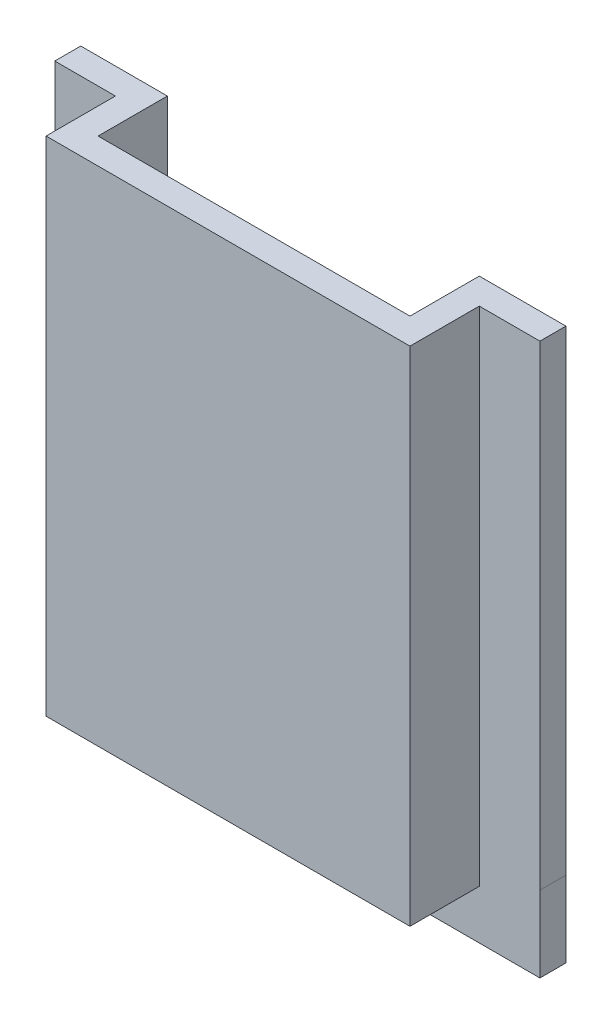
SolidWorks part; units mm, degrees
ref_plane "Front Plane" through (0, 0, 0) normal (0, 0, 1) x (1, 0, 0)
ref_plane "Top Plane" through (0, 0, 0) normal (0, 1, 0) x (1, 0, 0)
ref_plane "Right Plane" through (0, 0, 0) normal (1, 0, 0) x (0, 0, -1)
sketch "Sketch1" plane through (0, 0, 0) normal (0, 0, 1) x (1, 0, 0)
  line L1 (-21, 27.5) -> (21, 27.5)
  line L2 (-21, 27.5) -> (-21, -30.5)
  line L3 (-21, -30.5) -> (21, -30.5)
  line L4 (21, 27.5) -> (21, -30.5)
  dimension "D1" = 21
  dimension "D2" = 42
  dimension "D3" = 27.5
  dimension "D4" = 58
extrude "Boss-Extrude1" add sketch "Sketch1" along normal blind 3
sketch "Sketch2" plane through (0, 0, 0) normal (0, 0, -1) x (-1, 0, 0)
  line L0 (21, -30.5) -> (-21, -30.5) construction
  line L1 (-21, 27.5) -> (-18, 27.5)
  line L2 (-21, 27.5) -> (-21, -30.5)
  line L3 (-21, -30.5) -> (-18, -30.5)
  line L4 (-18, 27.5) -> (-18, -30.5)
  dimension "D1" = 3
extrude "Boss-Extrude2" add sketch "Sketch2" along normal blind 8
sketch "Sketch3" plane through (0, 0, 0) normal (0, 0, -1) x (-1, 0, 0)
  line L0 (21, -30.5) -> (-18, -30.5) construction
  line L1 (21, 27.5) -> (18, 27.5)
  line L2 (21, 27.5) -> (21, -30.5)
  line L3 (21, -30.5) -> (18, -30.5)
  line L4 (18, 27.5) -> (18, -30.5)
  dimension "D1" = 3
extrude "Boss-Extrude3" add sketch "Sketch3" along normal blind 8
sketch "Sketch4" plane through (0, 0, 0) normal (0, 0, -1) x (-1, 0, 0)
  line L1 (-18, -30.5) -> (18.0406, -30.5)
  line L2 (-18, -30.5) -> (-18, -26.1512)
  line L3 (-18, -26.1512) -> (18.0406, -26.1512)
  line L4 (18.0406, -30.5) -> (18.0406, -26.1512)
extrude "Boss-Extrude4" add sketch "Sketch4" along normal blind 8
sketch "Sketch5" plane through (0, 0, -8) normal (0, 0, -1) x (-1, 0, 0)
  line L1 (18, 27.5) -> (28, 27.5)
  line L2 (18, 27.5) -> (18, -26.1666)
  line L3 (18, -26.1666) -> (28, -26.1666)
  line L4 (28, 27.5) -> (28, -26.1666)
  dimension "D1" = 10
extrude "Boss-Extrude5" add sketch "Sketch5" against normal blind 3
sketch "Sketch6" plane through (0, 0, -8) normal (0, 0, -1) x (-1, 0, 0)
  line L1 (-18, 27.5) -> (-28, 27.5)
  line L2 (-18, 27.5) -> (-18, -27.3835)
  line L3 (-18, -27.3835) -> (-28, -27.3835)
  line L4 (-28, 27.5) -> (-28, -27.3835)
  dimension "D1" = 10
extrude "Boss-Extrude6" add sketch "Sketch6" against normal blind 3
sketch "Sketch7" plane through (0, 0, -8) normal (0, 0, -1) x (-1, 0, 0)
  line L1 (28, -26.1666) -> (-27.9972, -26.1666)
  line L2 (28, -26.1666) -> (28, -36.1666)
  line L3 (28, -36.1666) -> (-27.9972, -36.1666)
  line L4 (-27.9972, -26.1666) -> (-27.9972, -36.1666)
  dimension "D1" = 10
extrude "Boss-Extrude7" add sketch "Sketch7" against normal blind 3
